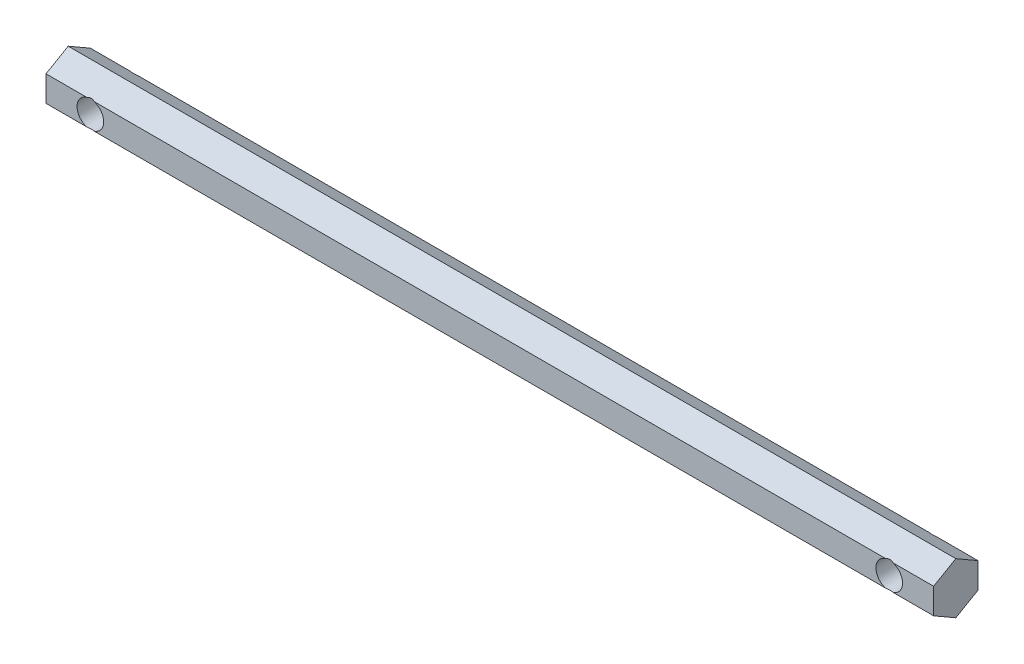
SolidWorks part; units mm, degrees
ref_plane "Plano frontal" through (0, 0, 0) normal (0, 0, 1) x (1, 0, 0)
ref_plane "Plano superior" through (0, 0, 0) normal (0, 1, 0) x (1, 0, 0)
ref_plane "Plano direito" through (0, 0, 0) normal (1, 0, 0) x (0, 0, -1)
sketch "Sketch1" plane through (0, 0, 0) normal (1, 0, 0) x (0, 0, -1)
  line L0 (-8.3414, 2.8868) -> (9.6861, 2.8868) construction
  line L1 (0, 5.7735) -> (-5, 2.8868)
  line L2 (-5, 2.8868) -> (-5, -2.8868)
  line L3 (-5, -2.8868) -> (0, -5.7735)
  line L4 (0, -5.7735) -> (5, -2.8868)
  line L5 (5, -2.8868) -> (5, 2.8868)
  line L6 (5, 2.8868) -> (0, 5.7735)
  line L7 (-8.3414, -2.8868) -> (9.6861, -2.8868) construction
  circle A0 centre (0, 0) radius 5 construction
  dimension "D1" = 10
extrude "Boss-Extrude1" add sketch "Sketch1" along normal mid plane 200
sketch "Sketch2" plane through (0, 0, 0) normal (0, 0, 1) x (1, 0, 0)
  line L0 (120.1463, 0) -> (-122.4896, 0) construction
  line L1 (0, 39.7277) -> (0, -43.0342) construction
  circle A0 centre (90, 0) radius 3
  circle A1 centre (-90, 0) radius 3
  dimension "D3" = 6
  dimension "D4" = 6
  dimension "D1" = 90
  dimension "D2" = 90
extrude "Cut-Extrude1" cut sketch "Sketch2" against normal through all both and the other way through all
